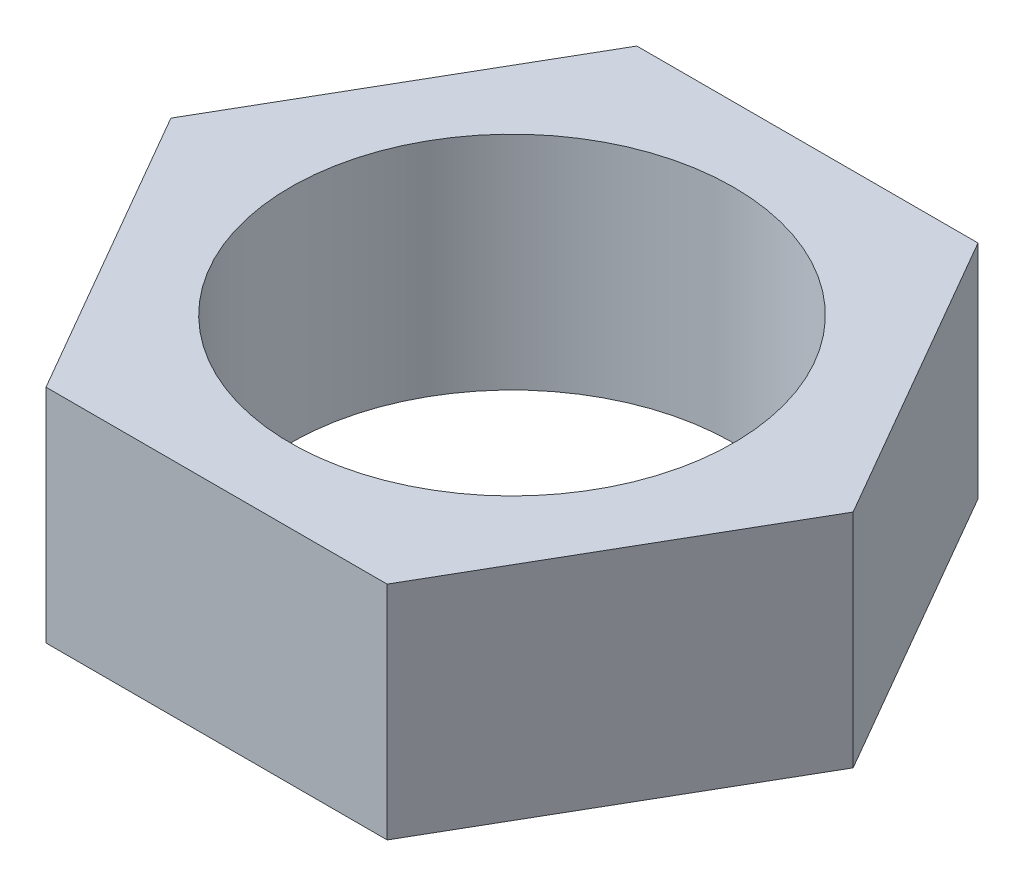
SolidWorks part; units mm, degrees
ref_plane "前基準面" through (0, 0, 0) normal (0, 0, 1) x (1, 0, 0)
ref_plane "上基準面" through (0, 0, 0) normal (0, 1, 0) x (1, 0, 0)
ref_plane "右基準面" through (0, 0, 0) normal (1, 0, 0) x (0, 0, -1)
sketch "草圖1" plane through (0, 0, 0) normal (0, 1, 0) x (1, 0, 0)
  line L1 (4.6188, 0) -> (2.3094, 4)
  line L2 (2.3094, 4) -> (-2.3094, 4)
  line L3 (-2.3094, 4) -> (-4.6188, 0)
  line L4 (-4.6188, 0) -> (-2.3094, -4)
  line L5 (-2.3094, -4) -> (2.3094, -4)
  line L6 (2.3094, -4) -> (4.6188, 0)
  circle A0 centre (0, 0) radius 4 construction
  dimension "D1" = 8
extrude "填料-伸長1" add sketch "草圖1" along normal blind 3
sketch "草圖2" plane through (0, 0, 0) normal (0, -1, 0) x (1, 0, 0)
  circle A0 centre (0, 0) radius 3
  dimension "D1" = 6
extrude "除料-伸長1" cut sketch "草圖2" against normal blind 3 contours A0
